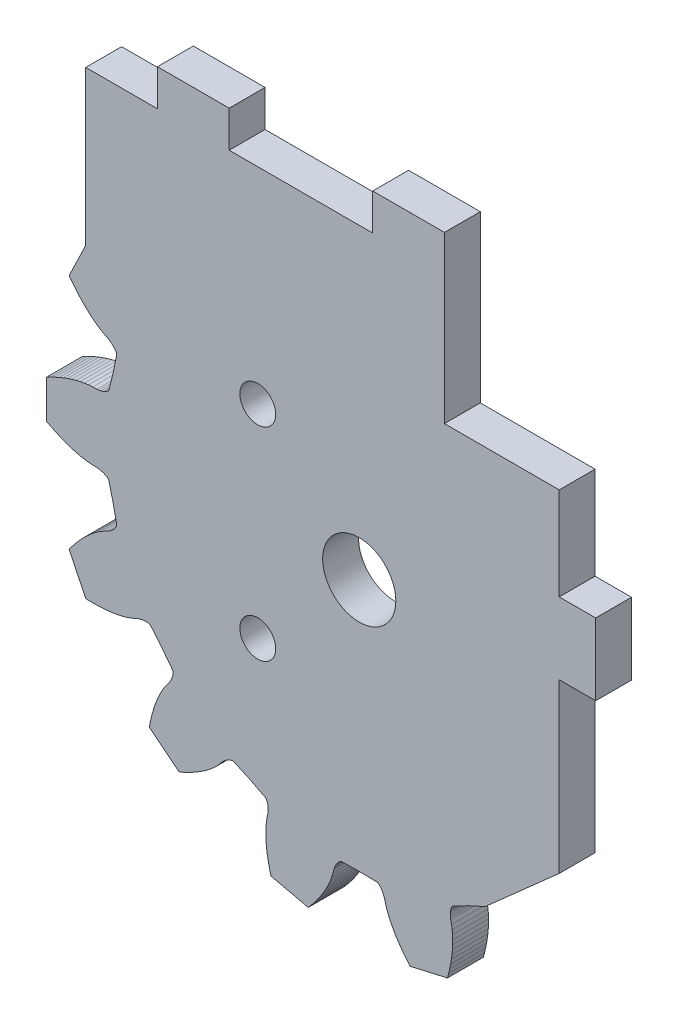
SolidWorks part; units mm, degrees
ref_plane "Front Plane" through (0, 0, 0) normal (0, 0, 1) x (1, 0, 0)
ref_plane "Top Plane" through (0, 0, 0) normal (0, 1, 0) x (1, 0, 0)
ref_plane "Right Plane" through (0, 0, 0) normal (1, 0, 0) x (0, 0, -1)
sketch "Sketch1" plane through (0, 0, 0) normal (0, 0, 1) x (1, 0, 0)
  line L0 (49.5201, 32.7081) -> (49.9074, 31.1602)
  line L1 (49.9074, 31.1602) -> (50.0141, 31.0551)
  line L2 (50.0141, 31.0551) -> (50.1157, 30.9819)
  line L3 (50.1157, 30.9819) -> (50.2145, 30.9258)
  line L4 (50.2145, 30.9258) -> (50.3116, 30.8811)
  line L5 (50.3116, 30.8811) -> (50.4073, 30.845)
  line L6 (50.4073, 30.845) -> (50.596, 30.7914)
  line L7 (50.596, 30.7914) -> (50.782, 30.7566)
  line L8 (50.782, 30.7566) -> (50.9659, 30.736)
  line L9 (50.9659, 30.736) -> (51.3296, 30.7264)
  line L10 (51.3296, 30.7264) -> (51.6946, 30.7028)
  line L11 (51.6946, 30.7028) -> (52.0629, 30.6532)
  line L12 (52.0629, 30.6532) -> (52.4332, 30.5824)
  line L13 (52.4332, 30.5824) -> (52.8051, 30.4927)
  line L14 (52.8051, 30.4927) -> (53.1779, 30.3858)
  line L15 (53.1779, 30.3858) -> (53.5516, 30.2626)
  line L16 (53.5516, 30.2626) -> (53.9257, 30.1241)
  line L17 (53.9257, 30.1241) -> (54.3001, 29.9707)
  line L18 (54.3001, 29.9707) -> (54.6743, 29.8031)
  line L19 (54.6743, 29.8031) -> (55.0479, 29.6212)
  line L20 (55.0479, 29.6212) -> (55.4208, 29.4262)
  line L21 (55.4208, 29.4262) -> (55.4208, 26.0462)
  line L22 (55.4208, 26.0462) -> (55.0479, 25.8511)
  line L23 (55.0479, 25.8511) -> (54.6743, 25.6692)
  line L24 (54.6743, 25.6692) -> (54.3001, 25.5016)
  line L25 (54.3001, 25.5016) -> (53.9257, 25.3482)
  line L26 (53.9257, 25.3482) -> (53.5516, 25.2098)
  line L27 (53.5516, 25.2098) -> (53.1779, 25.0866)
  line L28 (53.1779, 25.0866) -> (52.8051, 24.9796)
  line L29 (52.8051, 24.9796) -> (52.4332, 24.89)
  line L30 (52.4332, 24.89) -> (52.0629, 24.8191)
  line L31 (52.0629, 24.8191) -> (51.6946, 24.7693)
  line L32 (51.6946, 24.7693) -> (51.3296, 24.746)
  line L33 (51.3296, 24.746) -> (50.9659, 24.7363)
  line L34 (50.9659, 24.7363) -> (50.782, 24.7157)
  line L35 (50.782, 24.7157) -> (50.596, 24.6809)
  line L36 (50.596, 24.6809) -> (50.4073, 24.6273)
  line L37 (50.4073, 24.6273) -> (50.3116, 24.5913)
  line L38 (50.3116, 24.5913) -> (50.2145, 24.5466)
  line L39 (50.2145, 24.5466) -> (50.1157, 24.4904)
  line L40 (50.1157, 24.4904) -> (50.0141, 24.4173)
  line L41 (50.0141, 24.4173) -> (49.9074, 24.3121)
  line L42 (49.9074, 24.3121) -> (49.5201, 22.7642)
  line L43 (49.5201, 22.7642) -> (49.1973, 21.2014)
  line L44 (49.1973, 21.2014) -> (49.2481, 21.0604)
  line L45 (49.2481, 21.0604) -> (49.3077, 20.9502)
  line L46 (49.3077, 20.9502) -> (49.3725, 20.857)
  line L47 (49.3725, 20.857) -> (49.4406, 20.7747)
  line L48 (49.4406, 20.7747) -> (49.511, 20.7005)
  line L49 (49.511, 20.7005) -> (49.6578, 20.5702)
  line L50 (49.6578, 20.5702) -> (49.8102, 20.4582)
  line L51 (49.8102, 20.4582) -> (49.9669, 20.3601)
  line L52 (49.9669, 20.3601) -> (50.2905, 20.1935)
  line L53 (50.2905, 20.1935) -> (50.6092, 20.0139)
  line L54 (50.6092, 20.0139) -> (50.9194, 19.8095)
  line L55 (50.9194, 19.8095) -> (51.2224, 19.5849)
  line L56 (51.2224, 19.5849) -> (51.5183, 19.3429)
  line L57 (51.5183, 19.3429) -> (51.8081, 19.0845)
  line L58 (51.8081, 19.0845) -> (52.0913, 18.8115)
  line L59 (52.0913, 18.8115) -> (52.3682, 18.5242)
  line L60 (52.3682, 18.5242) -> (52.639, 18.2237)
  line L61 (52.639, 18.2237) -> (52.9034, 17.9103)
  line L62 (52.9034, 17.9103) -> (53.1612, 17.5844)
  line L63 (53.1612, 17.5844) -> (53.4124, 17.2469)
  line L64 (53.4124, 17.2469) -> (51.946, 14.2016)
  line L65 (51.946, 14.2016) -> (51.5252, 14.1877)
  line L66 (51.5252, 14.1877) -> (51.1099, 14.1862)
  line L67 (51.1099, 14.1862) -> (50.6999, 14.1973)
  line L68 (50.6999, 14.1973) -> (50.2961, 14.2215)
  line L69 (50.2961, 14.2215) -> (49.8991, 14.2591)
  line L70 (49.8991, 14.2591) -> (49.5089, 14.3101)
  line L71 (49.5089, 14.3101) -> (49.1264, 14.3756)
  line L72 (49.1264, 14.3756) -> (48.7525, 14.4562)
  line L73 (48.7525, 14.4562) -> (48.388, 14.5529)
  line L74 (48.388, 14.5529) -> (48.035, 14.668)
  line L75 (48.035, 14.668) -> (47.6956, 14.8054)
  line L76 (47.6956, 14.8054) -> (47.3636, 14.9542)
  line L77 (47.3636, 14.9542) -> (47.1891, 15.0157)
  line L78 (47.1891, 15.0157) -> (47.0065, 15.065)
  line L79 (47.0065, 15.065) -> (46.8135, 15.0985)
  line L80 (46.8135, 15.0985) -> (46.7114, 15.1074)
  line L81 (46.7114, 15.1074) -> (46.6047, 15.1094)
  line L82 (46.6047, 15.1094) -> (46.4914, 15.1018)
  line L83 (46.4914, 15.1018) -> (46.368, 15.0797)
  line L84 (46.368, 15.0797) -> (46.226, 15.0315)
  line L85 (46.226, 15.0315) -> (45.2056, 13.8049)
  line L86 (45.2056, 13.8049) -> (44.2366, 12.5369)
  line L87 (44.2366, 12.5369) -> (44.2211, 12.3878)
  line L88 (44.2211, 12.3878) -> (44.2272, 12.2626)
  line L89 (44.2272, 12.2626) -> (44.245, 12.1506)
  line L90 (44.245, 12.1506) -> (44.2707, 12.0467)
  line L91 (44.2707, 12.0467) -> (44.3019, 11.9494)
  line L92 (44.3019, 11.9494) -> (44.3776, 11.7686)
  line L93 (44.3776, 11.7686) -> (44.4663, 11.6014)
  line L94 (44.4663, 11.6014) -> (44.5651, 11.445)
  line L95 (44.5651, 11.445) -> (44.784, 11.1544)
  line L96 (44.784, 11.1544) -> (44.9936, 10.8544)
  line L97 (44.9936, 10.8544) -> (45.1843, 10.5357)
  line L98 (45.1843, 10.5357) -> (45.3598, 10.2019)
  line L99 (45.3598, 10.2019) -> (45.5214, 9.8552)
  line L100 (45.5214, 9.8552) -> (45.6705, 9.4971)
  line L101 (45.6705, 9.4971) -> (45.8071, 9.128)
  line L102 (45.8071, 9.128) -> (45.9321, 8.749)
  line L103 (45.9321, 8.749) -> (46.0456, 8.3609)
  line L104 (46.0456, 8.3609) -> (46.1477, 7.9637)
  line L105 (46.1477, 7.9637) -> (46.2387, 7.5583)
  line L106 (46.2387, 7.5583) -> (46.3184, 7.145)
  line L107 (46.3184, 7.145) -> (43.6761, 5.0378)
  line L108 (43.6761, 5.0378) -> (43.2907, 5.2075)
  line L109 (43.2907, 5.2075) -> (42.9158, 5.3866)
  line L110 (42.9158, 5.3866) -> (42.5516, 5.5745)
  line L111 (42.5516, 5.5745) -> (42.1983, 5.7714)
  line L112 (42.1983, 5.7714) -> (41.8567, 5.9776)
  line L113 (41.8567, 5.9776) -> (41.5272, 6.193)
  line L114 (41.5272, 6.193) -> (41.2112, 6.4178)
  line L115 (41.2112, 6.4178) -> (40.9092, 6.6528)
  line L116 (40.9092, 6.6528) -> (40.623, 6.8979)
  line L117 (40.623, 6.8979) -> (40.3545, 7.1549)
  line L118 (40.3545, 7.1549) -> (40.1086, 7.4259)
  line L119 (40.1086, 7.4259) -> (39.8742, 7.7041)
  line L120 (39.8742, 7.7041) -> (39.7436, 7.8351)
  line L121 (39.7436, 7.8351) -> (39.6004, 7.9588)
  line L122 (39.6004, 7.9588) -> (39.4409, 8.0729)
  line L123 (39.4409, 8.0729) -> (39.353, 8.125)
  line L124 (39.353, 8.125) -> (39.2575, 8.1732)
  line L125 (39.2575, 8.1732) -> (39.1521, 8.2154)
  line L126 (39.1521, 8.2154) -> (39.0314, 8.2492)
  line L127 (39.0314, 8.2492) -> (38.8826, 8.2672)
  line L128 (38.8826, 8.2672) -> (37.431, 7.6048)
  line L129 (37.431, 7.6048) -> (36.0081, 6.8829)
  line L130 (36.0081, 6.8829) -> (35.9293, 6.7551)
  line L131 (35.9293, 6.7551) -> (35.8803, 6.6398)
  line L132 (35.8803, 6.6398) -> (35.8478, 6.5311)
  line L133 (35.8478, 6.5311) -> (35.8257, 6.4265)
  line L134 (35.8257, 6.4265) -> (35.8117, 6.3251)
  line L135 (35.8117, 6.3251) -> (35.8016, 6.1293)
  line L136 (35.8016, 6.1293) -> (35.8089, 5.9403)
  line L137 (35.8089, 5.9403) -> (35.83, 5.7564)
  line L138 (35.83, 5.7564) -> (35.9014, 5.3998)
  line L139 (35.9014, 5.3998) -> (35.9598, 5.0386)
  line L140 (35.9598, 5.0386) -> (35.9933, 4.6685)
  line L141 (35.9933, 4.6685) -> (36.0065, 4.2918)
  line L142 (36.0065, 4.2918) -> (36.002, 3.9093)
  line L143 (36.002, 3.9093) -> (35.9806, 3.522)
  line L144 (35.9806, 3.522) -> (35.9438, 3.13)
  line L145 (35.9438, 3.13) -> (35.892, 2.7346)
  line L146 (35.892, 2.7346) -> (35.8257, 2.3355)
  line L147 (35.8257, 2.3355) -> (35.7454, 1.9334)
  line L148 (35.7454, 1.9334) -> (35.6514, 1.5288)
  line L149 (35.6514, 1.5288) -> (35.544, 1.1217)
  line L150 (35.544, 1.1217) -> (32.2491, 0.3696)
  line L151 (32.2491, 0.3696) -> (31.9758, 0.6896)
  line L152 (31.9758, 0.6896) -> (31.7155, 1.0137)
  line L153 (31.7155, 1.0137) -> (31.4688, 1.3411)
  line L154 (31.4688, 1.3411) -> (31.2359, 1.6718)
  line L155 (31.2359, 1.6718) -> (31.0175, 2.0058)
  line L156 (31.0175, 2.0058) -> (30.8143, 2.3426)
  line L157 (30.8143, 2.3426) -> (30.6271, 2.6825)
  line L158 (30.6271, 2.6825) -> (30.4569, 3.0251)
  line L159 (30.4569, 3.0251) -> (30.3055, 3.3703)
  line L160 (30.3055, 3.3703) -> (30.1752, 3.7181)
  line L161 (30.1752, 3.7181) -> (30.0711, 4.0691)
  line L162 (30.0711, 4.0691) -> (29.9806, 4.4214)
  line L163 (29.9806, 4.4214) -> (29.9197, 4.5961)
  line L164 (29.9197, 4.5961) -> (29.8445, 4.7696)
  line L165 (29.8445, 4.7696) -> (29.7503, 4.9416)
  line L166 (29.7503, 4.9416) -> (29.6936, 5.0269)
  line L167 (29.6936, 5.0269) -> (29.6283, 5.1115)
  line L168 (29.6283, 5.1115) -> (29.5519, 5.1953)
  line L169 (29.5519, 5.1953) -> (29.4577, 5.2781)
  line L170 (29.4577, 5.2781) -> (29.3314, 5.3589)
  line L171 (29.3314, 5.3589) -> (27.736, 5.3919)
  line L172 (27.736, 5.3919) -> (26.1409, 5.3589)
  line L173 (26.1409, 5.3589) -> (26.0147, 5.2781)
  line L174 (26.0147, 5.2781) -> (25.9204, 5.1953)
  line L175 (25.9204, 5.1953) -> (25.8437, 5.1115)
  line L176 (25.8437, 5.1115) -> (25.7787, 5.0269)
  line L177 (25.7787, 5.0269) -> (25.7221, 4.9416)
  line L178 (25.7221, 4.9416) -> (25.6278, 4.7696)
  line L179 (25.6278, 4.7696) -> (25.5527, 4.5961)
  line L180 (25.5527, 4.5961) -> (25.4917, 4.4214)
  line L181 (25.4917, 4.4214) -> (25.4013, 4.0691)
  line L182 (25.4013, 4.0691) -> (25.2971, 3.7181)
  line L183 (25.2971, 3.7181) -> (25.1668, 3.3703)
  line L184 (25.1668, 3.3703) -> (25.0154, 3.0251)
  line L185 (25.0154, 3.0251) -> (24.8453, 2.6825)
  line L186 (24.8453, 2.6825) -> (24.6581, 2.3426)
  line L187 (24.6581, 2.3426) -> (24.4549, 2.0058)
  line L188 (24.4549, 2.0058) -> (24.2364, 1.6718)
  line L189 (24.2364, 1.6718) -> (24.0035, 1.3411)
  line L190 (24.0035, 1.3411) -> (23.7569, 1.0137)
  line L191 (23.7569, 1.0137) -> (23.4965, 0.6896)
  line L192 (23.4965, 0.6896) -> (23.2232, 0.3696)
  line L193 (23.2232, 0.3696) -> (19.9283, 1.1217)
  line L194 (19.9283, 1.1217) -> (19.8209, 1.5288)
  line L195 (19.8209, 1.5288) -> (19.7269, 1.9334)
  line L196 (19.7269, 1.9334) -> (19.6466, 2.3355)
  line L197 (19.6466, 2.3355) -> (19.5804, 2.7346)
  line L198 (19.5804, 2.7346) -> (19.5285, 3.13)
  line L199 (19.5285, 3.13) -> (19.4917, 3.522)
  line L200 (19.4917, 3.522) -> (19.4704, 3.9093)
  line L201 (19.4704, 3.9093) -> (19.4658, 4.2918)
  line L202 (19.4658, 4.2918) -> (19.479, 4.6685)
  line L203 (19.479, 4.6685) -> (19.5125, 5.0386)
  line L204 (19.5125, 5.0386) -> (19.571, 5.3998)
  line L205 (19.571, 5.3998) -> (19.6423, 5.7564)
  line L206 (19.6423, 5.7564) -> (19.6634, 5.9403)
  line L207 (19.6634, 5.9403) -> (19.6708, 6.1293)
  line L208 (19.6708, 6.1293) -> (19.6606, 6.3251)
  line L209 (19.6606, 6.3251) -> (19.6466, 6.4265)
  line L210 (19.6466, 6.4265) -> (19.6245, 6.5311)
  line L211 (19.6245, 6.5311) -> (19.592, 6.6398)
  line L212 (19.592, 6.6398) -> (19.543, 6.7551)
  line L213 (19.543, 6.7551) -> (19.4643, 6.8829)
  line L214 (19.4643, 6.8829) -> (18.0414, 7.6048)
  line L215 (18.0414, 7.6048) -> (16.5898, 8.2672)
  line L216 (16.5898, 8.2672) -> (16.4409, 8.2492)
  line L217 (16.4409, 8.2492) -> (16.3203, 8.2154)
  line L218 (16.3203, 8.2154) -> (16.2149, 8.1732)
  line L219 (16.2149, 8.1732) -> (16.1193, 8.125)
  line L220 (16.1193, 8.125) -> (16.0315, 8.0729)
  line L221 (16.0315, 8.0729) -> (15.872, 7.9588)
  line L222 (15.872, 7.9588) -> (15.7287, 7.8351)
  line L223 (15.7287, 7.8351) -> (15.5981, 7.7041)
  line L224 (15.5981, 7.7041) -> (15.3637, 7.4259)
  line L225 (15.3637, 7.4259) -> (15.1178, 7.1549)
  line L226 (15.1178, 7.1549) -> (14.8493, 6.8979)
  line L227 (14.8493, 6.8979) -> (14.5631, 6.6528)
  line L228 (14.5631, 6.6528) -> (14.2611, 6.4178)
  line L229 (14.2611, 6.4178) -> (13.9451, 6.193)
  line L230 (13.9451, 6.193) -> (13.6157, 5.9776)
  line L231 (13.6157, 5.9776) -> (13.274, 5.7714)
  line L232 (13.274, 5.7714) -> (12.9207, 5.5745)
  line L233 (12.9207, 5.5745) -> (12.5565, 5.3866)
  line L234 (12.5565, 5.3866) -> (12.1816, 5.2075)
  line L235 (12.1816, 5.2075) -> (11.7963, 5.0378)
  line L236 (11.7963, 5.0378) -> (9.1539, 7.145)
  line L237 (9.1539, 7.145) -> (9.2337, 7.5583)
  line L238 (9.2337, 7.5583) -> (9.3246, 7.9637)
  line L239 (9.3246, 7.9637) -> (9.4267, 8.3609)
  line L240 (9.4267, 8.3609) -> (9.5402, 8.749)
  line L241 (9.5402, 8.749) -> (9.6652, 9.128)
  line L242 (9.6652, 9.128) -> (9.8019, 9.4971)
  line L243 (9.8019, 9.4971) -> (9.951, 9.8552)
  line L244 (9.951, 9.8552) -> (10.1125, 10.2019)
  line L245 (10.1125, 10.2019) -> (10.288, 10.5357)
  line L246 (10.288, 10.5357) -> (10.4788, 10.8544)
  line L247 (10.4788, 10.8544) -> (10.6883, 11.1544)
  line L248 (10.6883, 11.1544) -> (10.9073, 11.445)
  line L249 (10.9073, 11.445) -> (11.0058, 11.6014)
  line L250 (11.0058, 11.6014) -> (11.0947, 11.7686)
  line L251 (11.0947, 11.7686) -> (11.1704, 11.9494)
  line L252 (11.1704, 11.9494) -> (11.2017, 12.0467)
  line L253 (11.2017, 12.0467) -> (11.2273, 12.1506)
  line L254 (11.2273, 12.1506) -> (11.2451, 12.2626)
  line L255 (11.2451, 12.2626) -> (11.2512, 12.3878)
  line L256 (11.2512, 12.3878) -> (11.2354, 12.5369)
  line L257 (11.2354, 12.5369) -> (10.2667, 13.8049)
  line L258 (10.2667, 13.8049) -> (9.2464, 15.0315)
  line L259 (9.2464, 15.0315) -> (9.1044, 15.0797)
  line L260 (9.1044, 15.0797) -> (8.9809, 15.1018)
  line L261 (8.9809, 15.1018) -> (8.8676, 15.1094)
  line L262 (8.8676, 15.1094) -> (8.761, 15.1074)
  line L263 (8.761, 15.1074) -> (8.6589, 15.0985)
  line L264 (8.6589, 15.0985) -> (8.4658, 15.065)
  line L265 (8.4658, 15.065) -> (8.2832, 15.0157)
  line L266 (8.2832, 15.0157) -> (8.1087, 14.9542)
  line L267 (8.1087, 14.9542) -> (7.7767, 14.8054)
  line L268 (7.7767, 14.8054) -> (7.4374, 14.668)
  line L269 (7.4374, 14.668) -> (7.0843, 14.5529)
  line L270 (7.0843, 14.5529) -> (6.7198, 14.4562)
  line L271 (6.7198, 14.4562) -> (6.3459, 14.3756)
  line L272 (6.3459, 14.3756) -> (5.9634, 14.3101)
  line L273 (5.9634, 14.3101) -> (5.5733, 14.2591)
  line L274 (5.5733, 14.2591) -> (5.1763, 14.2215)
  line L275 (5.1763, 14.2215) -> (4.7724, 14.1973)
  line L276 (4.7724, 14.1973) -> (4.3624, 14.1862)
  line L277 (4.3624, 14.1862) -> (3.9472, 14.1877)
  line L278 (3.9472, 14.1877) -> (3.5263, 14.2016)
  line L279 (3.5263, 14.2016) -> (2.0599, 17.2469)
  line L280 (2.0599, 17.2469) -> (2.3111, 17.5844)
  line L281 (2.3111, 17.5844) -> (2.569, 17.9103)
  line L282 (2.569, 17.9103) -> (2.8334, 18.2237)
  line L283 (2.8334, 18.2237) -> (3.1041, 18.5242)
  line L284 (3.1041, 18.5242) -> (3.381, 18.8115)
  line L285 (3.381, 18.8115) -> (3.6642, 19.0845)
  line L286 (3.6642, 19.0845) -> (3.954, 19.3429)
  line L287 (3.954, 19.3429) -> (4.2499, 19.5849)
  line L288 (4.2499, 19.5849) -> (4.553, 19.8095)
  line L289 (4.553, 19.8095) -> (4.8631, 20.0139)
  line L290 (4.8631, 20.0139) -> (5.1819, 20.1935)
  line L291 (5.1819, 20.1935) -> (5.5054, 20.3601)
  line L292 (5.5054, 20.3601) -> (5.6622, 20.4582)
  line L293 (5.6622, 20.4582) -> (5.8146, 20.5702)
  line L294 (5.8146, 20.5702) -> (5.9614, 20.7005)
  line L295 (5.9614, 20.7005) -> (6.0317, 20.7747)
  line L296 (6.0317, 20.7747) -> (6.0998, 20.857)
  line L297 (6.0998, 20.857) -> (6.1646, 20.9502)
  line L298 (6.1646, 20.9502) -> (6.2243, 21.0604)
  line L299 (6.2243, 21.0604) -> (6.2748, 21.2014)
  line L300 (6.2748, 21.2014) -> (5.9522, 22.7642)
  line L301 (5.9522, 22.7642) -> (5.5649, 24.3121)
  line L302 (5.5649, 24.3121) -> (5.4582, 24.4173)
  line L303 (5.4582, 24.4173) -> (5.3566, 24.4904)
  line L304 (5.3566, 24.4904) -> (5.2578, 24.5466)
  line L305 (5.2578, 24.5466) -> (5.1608, 24.5913)
  line L306 (5.1608, 24.5913) -> (5.065, 24.6273)
  line L307 (5.065, 24.6273) -> (4.8763, 24.6809)
  line L308 (4.8763, 24.6809) -> (4.6904, 24.7157)
  line L309 (4.6904, 24.7157) -> (4.5065, 24.7363)
  line L310 (4.5065, 24.7363) -> (4.1427, 24.746)
  line L311 (4.1427, 24.746) -> (3.7777, 24.7693)
  line L312 (3.7777, 24.7693) -> (3.4094, 24.8191)
  line L313 (3.4094, 24.8191) -> (3.0391, 24.89)
  line L314 (3.0391, 24.89) -> (2.6673, 24.9796)
  line L315 (2.6673, 24.9796) -> (2.2944, 25.0866)
  line L316 (2.2944, 25.0866) -> (1.9207, 25.2098)
  line L317 (1.9207, 25.2098) -> (1.5466, 25.3482)
  line L318 (1.5466, 25.3482) -> (1.1722, 25.5016)
  line L319 (1.1722, 25.5016) -> (0.7981, 25.6692)
  line L320 (0.7981, 25.6692) -> (0.4244, 25.8511)
  line L321 (0.4244, 25.8511) -> (0.0516, 26.0462)
  line L322 (0.0516, 26.0462) -> (0.0516, 29.4262)
  line L323 (0.0516, 29.4262) -> (0.4244, 29.6212)
  line L324 (0.4244, 29.6212) -> (0.7981, 29.8031)
  line L325 (0.7981, 29.8031) -> (1.1722, 29.9707)
  line L326 (1.1722, 29.9707) -> (1.5466, 30.1241)
  line L327 (1.5466, 30.1241) -> (1.9207, 30.2626)
  line L328 (1.9207, 30.2626) -> (2.2944, 30.3858)
  line L329 (2.2944, 30.3858) -> (2.6673, 30.4927)
  line L330 (2.6673, 30.4927) -> (3.0391, 30.5824)
  line L331 (3.0391, 30.5824) -> (3.4094, 30.6532)
  line L332 (3.4094, 30.6532) -> (3.7777, 30.7028)
  line L333 (3.7777, 30.7028) -> (4.1427, 30.7264)
  line L334 (4.1427, 30.7264) -> (4.5065, 30.736)
  line L335 (4.5065, 30.736) -> (4.6904, 30.7566)
  line L336 (4.6904, 30.7566) -> (4.8763, 30.7914)
  line L337 (4.8763, 30.7914) -> (5.065, 30.845)
  line L338 (5.065, 30.845) -> (5.1608, 30.8811)
  line L339 (5.1608, 30.8811) -> (5.2578, 30.9258)
  line L340 (5.2578, 30.9258) -> (5.3566, 30.9819)
  line L341 (5.3566, 30.9819) -> (5.4582, 31.0551)
  line L342 (5.4582, 31.0551) -> (5.5649, 31.1602)
  line L343 (5.5649, 31.1602) -> (5.9522, 32.7081)
  line L344 (5.9522, 32.7081) -> (6.2748, 34.2709)
  line L345 (6.2748, 34.2709) -> (6.2243, 34.4119)
  line L346 (6.2243, 34.4119) -> (6.1646, 34.5222)
  line L347 (6.1646, 34.5222) -> (6.0998, 34.6154)
  line L348 (6.0998, 34.6154) -> (6.0317, 34.6977)
  line L349 (6.0317, 34.6977) -> (5.9614, 34.7718)
  line L350 (5.9614, 34.7718) -> (5.8146, 34.9021)
  line L351 (5.8146, 34.9021) -> (5.6622, 35.0142)
  line L352 (5.6622, 35.0142) -> (5.5054, 35.1122)
  line L353 (5.5054, 35.1122) -> (5.1819, 35.2788)
  line L354 (5.1819, 35.2788) -> (4.8631, 35.4584)
  line L355 (4.8631, 35.4584) -> (4.553, 35.6629)
  line L356 (4.553, 35.6629) -> (4.2499, 35.8874)
  line L357 (4.2499, 35.8874) -> (3.954, 36.1295)
  line L358 (3.954, 36.1295) -> (3.6642, 36.3878)
  line L359 (3.6642, 36.3878) -> (3.381, 36.6608)
  line L360 (3.381, 36.6608) -> (3.1041, 36.9481)
  line L361 (3.1041, 36.9481) -> (2.8334, 37.2486)
  line L362 (2.8334, 37.2486) -> (2.569, 37.562)
  line L363 (2.569, 37.562) -> (2.3111, 37.8879)
  line L364 (2.3111, 37.8879) -> (2.0599, 38.2255)
  line L365 (2.0599, 38.2255) -> (3.5263, 41.2707)
  line L366 (3.5263, 41.2707) -> (3.9472, 41.2847)
  line L367 (3.9472, 41.2847) -> (4.3624, 41.2862)
  line L368 (4.3624, 41.2862) -> (4.7724, 41.275)
  line L369 (4.7724, 41.275) -> (5.1763, 41.2509)
  line L370 (5.1763, 41.2509) -> (5.5733, 41.2133)
  line L371 (5.5733, 41.2133) -> (5.9634, 41.1622)
  line L372 (5.9634, 41.1622) -> (6.3459, 41.0967)
  line L373 (6.3459, 41.0967) -> (6.7198, 41.0162)
  line L374 (6.7198, 41.0162) -> (7.0843, 40.9194)
  line L375 (7.0843, 40.9194) -> (7.4374, 40.8043)
  line L376 (7.4374, 40.8043) -> (7.7767, 40.6669)
  line L377 (7.7767, 40.6669) -> (8.1087, 40.5181)
  line L378 (8.1087, 40.5181) -> (8.2832, 40.4566)
  line L379 (8.2832, 40.4566) -> (8.4658, 40.4073)
  line L380 (8.4658, 40.4073) -> (8.6589, 40.3738)
  line L381 (8.6589, 40.3738) -> (8.761, 40.3649)
  line L382 (8.761, 40.3649) -> (8.8676, 40.3629)
  line L383 (8.8676, 40.3629) -> (8.9809, 40.3705)
  line L384 (8.9809, 40.3705) -> (9.1044, 40.3926)
  line L385 (9.1044, 40.3926) -> (9.2464, 40.4409)
  line L386 (9.2464, 40.4409) -> (10.2667, 41.6674)
  line L387 (10.2667, 41.6674) -> (11.2354, 42.9354)
  line L388 (11.2354, 42.9354) -> (11.2512, 43.0845)
  line L389 (11.2512, 43.0845) -> (11.2451, 43.2097)
  line L390 (11.2451, 43.2097) -> (11.2273, 43.3217)
  line L391 (11.2273, 43.3217) -> (11.2017, 43.4256)
  line L392 (11.2017, 43.4256) -> (11.1704, 43.5229)
  line L393 (11.1704, 43.5229) -> (11.0947, 43.7037)
  line L394 (11.0947, 43.7037) -> (11.0058, 43.8709)
  line L395 (11.0058, 43.8709) -> (10.9073, 44.0273)
  line L396 (10.9073, 44.0273) -> (10.6883, 44.3179)
  line L397 (10.6883, 44.3179) -> (10.4788, 44.6179)
  line L398 (10.4788, 44.6179) -> (10.288, 44.9367)
  line L399 (10.288, 44.9367) -> (10.1125, 45.2704)
  line L400 (10.1125, 45.2704) -> (9.951, 45.6171)
  line L401 (9.951, 45.6171) -> (9.8019, 45.9753)
  line L402 (9.8019, 45.9753) -> (9.6652, 46.3443)
  line L403 (9.6652, 46.3443) -> (9.5402, 46.7233)
  line L404 (9.5402, 46.7233) -> (9.4267, 47.1114)
  line L405 (9.4267, 47.1114) -> (9.3246, 47.5087)
  line L406 (9.3246, 47.5087) -> (9.2337, 47.9141)
  line L407 (9.2337, 47.9141) -> (9.1539, 48.3273)
  line L408 (9.1539, 48.3273) -> (11.7963, 50.4345)
  line L409 (11.7963, 50.4345) -> (12.1816, 50.2648)
  line L410 (12.1816, 50.2648) -> (12.5565, 50.0858)
  line L411 (12.5565, 50.0858) -> (12.9207, 49.8978)
  line L412 (12.9207, 49.8978) -> (13.274, 49.7009)
  line L413 (13.274, 49.7009) -> (13.6157, 49.4947)
  line L414 (13.6157, 49.4947) -> (13.9451, 49.2793)
  line L415 (13.9451, 49.2793) -> (14.2611, 49.0545)
  line L416 (14.2611, 49.0545) -> (14.5631, 48.8196)
  line L417 (14.5631, 48.8196) -> (14.8493, 48.5745)
  line L418 (14.8493, 48.5745) -> (15.1178, 48.3174)
  line L419 (15.1178, 48.3174) -> (15.3637, 48.0464)
  line L420 (15.3637, 48.0464) -> (15.5981, 47.7683)
  line L421 (15.5981, 47.7683) -> (15.7287, 47.6372)
  line L422 (15.7287, 47.6372) -> (15.872, 47.5135)
  line L423 (15.872, 47.5135) -> (16.0315, 47.3994)
  line L424 (16.0315, 47.3994) -> (16.1193, 47.3471)
  line L425 (16.1193, 47.3471) -> (16.2149, 47.2991)
  line L426 (16.2149, 47.2991) -> (16.3203, 47.257)
  line L427 (16.3203, 47.257) -> (16.4409, 47.2232)
  line L428 (16.4409, 47.2232) -> (16.5898, 47.2051)
  line L429 (16.5898, 47.2051) -> (18.0414, 47.8676)
  line L430 (18.0414, 47.8676) -> (19.4643, 48.5894)
  line L431 (19.4643, 48.5894) -> (19.543, 48.7172)
  line L432 (19.543, 48.7172) -> (19.592, 48.8325)
  line L433 (19.592, 48.8325) -> (19.6245, 48.9412)
  line L434 (19.6245, 48.9412) -> (19.6466, 49.0459)
  line L435 (19.6466, 49.0459) -> (19.6606, 49.1472)
  line L436 (19.6606, 49.1472) -> (19.6708, 49.3431)
  line L437 (19.6708, 49.3431) -> (19.6634, 49.532)
  line L438 (19.6634, 49.532) -> (19.6423, 49.7159)
  line L439 (19.6423, 49.7159) -> (19.571, 50.0725)
  line L440 (19.571, 50.0725) -> (19.5125, 50.4337)
  line L441 (19.5125, 50.4337) -> (19.479, 50.8038)
  line L442 (19.479, 50.8038) -> (19.4658, 51.1805)
  line L443 (19.4658, 51.1805) -> (19.4704, 51.563)
  line L444 (19.4704, 51.563) -> (19.4917, 51.9504)
  line L445 (19.4917, 51.9504) -> (19.5285, 52.3423)
  line L446 (19.5285, 52.3423) -> (19.5804, 52.7378)
  line L447 (19.5804, 52.7378) -> (19.8209, 52.7378)
  line L448 (19.8209, 52.7378) -> (20.3725, 53.1297)
  line L449 (20.3725, 53.1297) -> (21.0344, 53.4665)
  line L450 (21.0344, 53.4665) -> (21.4927, 53.8005)
  line L451 (21.4927, 53.8005) -> (22.3582, 54.1312)
  line L452 (22.3582, 54.1312) -> (23.2232, 54.1312)
  line L453 (23.2232, 54.1312) -> (23.7569, 54.1312)
  line L454 (23.7569, 54.1312) -> (24.0035, 54.1312)
  line L455 (24.0035, 54.1312) -> (24.2364, 53.8005)
  line L456 (24.2364, 53.8005) -> (24.4549, 53.4665)
  line L457 (24.4549, 53.4665) -> (24.6581, 53.1297)
  line L458 (24.6581, 53.1297) -> (24.8453, 52.7898)
  line L459 (24.8453, 52.7898) -> (25.0154, 52.4472)
  line L460 (25.0154, 52.4472) -> (25.1668, 52.102)
  line L461 (25.1668, 52.102) -> (25.2971, 51.754)
  line L462 (25.2971, 51.754) -> (25.4013, 51.4033)
  line L463 (25.4013, 51.4033) -> (25.4917, 51.051)
  line L464 (25.4917, 51.051) -> (25.5527, 50.8762)
  line L465 (25.5527, 50.8762) -> (25.6278, 50.7027)
  line L466 (25.6278, 50.7027) -> (25.7221, 50.5308)
  line L467 (25.7221, 50.5308) -> (25.7787, 50.4454)
  line L468 (25.7787, 50.4454) -> (25.8437, 50.3608)
  line L469 (25.8437, 50.3608) -> (25.9204, 50.277)
  line L470 (25.9204, 50.277) -> (26.0147, 50.1942)
  line L471 (26.0147, 50.1942) -> (26.1409, 50.1134)
  line L472 (26.1409, 50.1134) -> (27.736, 50.0804)
  line L473 (27.736, 50.0804) -> (29.3314, 50.1134)
  line L474 (29.3314, 50.1134) -> (29.4577, 50.1942)
  line L475 (29.4577, 50.1942) -> (29.5519, 50.277)
  line L476 (29.5519, 50.277) -> (29.6283, 50.3608)
  line L477 (29.6283, 50.3608) -> (29.6936, 50.4454)
  line L478 (29.6936, 50.4454) -> (29.7503, 50.5308)
  line L479 (29.7503, 50.5308) -> (29.8445, 50.7027)
  line L480 (29.8445, 50.7027) -> (29.9197, 50.8762)
  line L481 (29.9197, 50.8762) -> (29.9806, 51.051)
  line L482 (29.9806, 51.051) -> (30.0711, 51.4033)
  line L483 (30.0711, 51.4033) -> (30.1752, 51.754)
  line L484 (30.1752, 51.754) -> (30.3055, 52.102)
  line L485 (30.3055, 52.102) -> (30.4569, 52.4472)
  line L486 (30.4569, 52.4472) -> (30.6271, 52.7898)
  line L487 (30.6271, 52.7898) -> (30.8143, 53.1297)
  line L488 (30.8143, 53.1297) -> (31.0175, 53.4665)
  line L489 (31.0175, 53.4665) -> (31.2359, 53.8005)
  line L490 (31.2359, 53.8005) -> (31.4688, 54.1312)
  line L491 (31.4688, 54.1312) -> (31.9758, 53.8005)
  line L492 (31.9758, 53.8005) -> (32.7958, 53.8005)
  line L493 (32.7958, 53.8005) -> (33.7632, 53.8005)
  line L494 (33.7632, 53.8005) -> (34.6287, 53.8005)
  line L495 (34.6287, 53.8005) -> (35.4434, 53.6108)
  line L496 (35.4434, 53.6108) -> (35.7454, 53.5389)
  line L497 (35.7454, 53.5389) -> (35.8257, 53.1368)
  line L498 (35.8257, 53.1368) -> (35.892, 52.7378)
  line L499 (35.892, 52.7378) -> (35.9438, 52.3423)
  line L500 (35.9438, 52.3423) -> (35.9806, 51.9504)
  line L501 (35.9806, 51.9504) -> (36.002, 51.563)
  line L502 (36.002, 51.563) -> (36.0065, 51.1805)
  line L503 (36.0065, 51.1805) -> (35.9933, 50.8038)
  line L504 (35.9933, 50.8038) -> (35.9598, 50.4337)
  line L505 (35.9598, 50.4337) -> (35.9014, 50.0725)
  line L506 (35.9014, 50.0725) -> (35.83, 49.7159)
  line L507 (35.83, 49.7159) -> (35.8089, 49.532)
  line L508 (35.8089, 49.532) -> (35.8016, 49.3431)
  line L509 (35.8016, 49.3431) -> (35.8117, 49.1472)
  line L510 (35.8117, 49.1472) -> (35.8257, 49.0459)
  line L511 (35.8257, 49.0459) -> (35.8478, 48.9412)
  line L512 (35.8478, 48.9412) -> (35.8803, 48.8325)
  line L513 (35.8803, 48.8325) -> (35.9293, 48.7172)
  line L514 (35.9293, 48.7172) -> (36.0081, 48.5894)
  line L515 (36.0081, 48.5894) -> (37.431, 47.8676)
  line L516 (37.431, 47.8676) -> (38.8826, 47.2051)
  line L517 (38.8826, 47.2051) -> (39.0314, 47.2232)
  line L518 (39.0314, 47.2232) -> (39.1521, 47.257)
  line L519 (39.1521, 47.257) -> (39.2575, 47.2991)
  line L520 (39.2575, 47.2991) -> (39.353, 47.3471)
  line L521 (39.353, 47.3471) -> (39.4409, 47.3994)
  line L522 (39.4409, 47.3994) -> (39.6004, 47.5135)
  line L523 (39.6004, 47.5135) -> (39.7436, 47.6372)
  line L524 (39.7436, 47.6372) -> (39.8742, 47.7683)
  line L525 (39.8742, 47.7683) -> (40.1086, 48.0464)
  line L526 (40.1086, 48.0464) -> (40.3545, 48.3174)
  line L527 (40.3545, 48.3174) -> (40.623, 48.5745)
  line L528 (40.623, 48.5745) -> (40.9092, 48.8196)
  line L529 (40.9092, 48.8196) -> (41.2112, 49.0545)
  line L530 (41.2112, 49.0545) -> (41.5272, 49.2793)
  line L531 (41.5272, 49.2793) -> (41.8567, 49.4947)
  line L532 (41.8567, 49.4947) -> (42.1983, 49.7009)
  line L533 (42.1983, 49.7009) -> (42.5516, 49.8978)
  line L534 (42.5516, 49.8978) -> (42.9158, 50.0858)
  line L535 (42.9158, 50.0858) -> (43.2907, 50.2648)
  line L536 (43.2907, 50.2648) -> (43.6761, 50.4345)
  line L537 (43.6761, 50.4345) -> (46.3184, 48.3273)
  line L538 (46.3184, 48.3273) -> (46.2387, 47.9141)
  line L539 (46.2387, 47.9141) -> (46.1477, 47.5087)
  line L540 (46.1477, 47.5087) -> (46.0456, 47.1114)
  line L541 (46.0456, 47.1114) -> (45.9321, 46.7233)
  line L542 (45.9321, 46.7233) -> (45.8071, 46.3443)
  line L543 (45.8071, 46.3443) -> (45.6705, 45.9753)
  line L544 (45.6705, 45.9753) -> (45.5214, 45.6171)
  line L545 (45.5214, 45.6171) -> (45.3598, 45.2704)
  line L546 (45.3598, 45.2704) -> (45.1843, 44.9367)
  line L547 (45.1843, 44.9367) -> (44.9936, 44.6179)
  line L548 (44.9936, 44.6179) -> (44.784, 44.3179)
  line L549 (44.784, 44.3179) -> (44.5651, 44.0273)
  line L550 (44.5651, 44.0273) -> (44.4663, 43.8709)
  line L551 (44.4663, 43.8709) -> (44.3776, 43.7037)
  line L552 (44.3776, 43.7037) -> (44.3019, 43.5229)
  line L553 (44.3019, 43.5229) -> (44.2707, 43.4256)
  line L554 (44.2707, 43.4256) -> (44.245, 43.3217)
  line L555 (44.245, 43.3217) -> (44.2272, 43.2097)
  line L556 (44.2272, 43.2097) -> (44.2211, 43.0845)
  line L557 (44.2211, 43.0845) -> (44.2366, 42.9354)
  line L558 (44.2366, 42.9354) -> (45.2056, 41.6674)
  line L559 (45.2056, 41.6674) -> (46.226, 40.4409)
  line L560 (46.226, 40.4409) -> (46.368, 40.3926)
  line L561 (46.368, 40.3926) -> (46.4914, 40.3705)
  line L562 (46.4914, 40.3705) -> (46.6047, 40.3629)
  line L563 (46.6047, 40.3629) -> (46.7114, 40.3649)
  line L564 (46.7114, 40.3649) -> (46.8135, 40.3738)
  line L565 (46.8135, 40.3738) -> (47.0065, 40.4073)
  line L566 (47.0065, 40.4073) -> (47.1891, 40.4566)
  line L567 (47.1891, 40.4566) -> (47.3636, 40.5181)
  line L568 (47.3636, 40.5181) -> (47.6956, 40.6669)
  line L569 (47.6956, 40.6669) -> (48.035, 40.8043)
  line L570 (48.035, 40.8043) -> (48.388, 40.9194)
  line L571 (48.388, 40.9194) -> (48.7525, 41.0162)
  line L572 (48.7525, 41.0162) -> (49.1264, 41.0967)
  line L573 (49.1264, 41.0967) -> (49.5089, 41.1622)
  line L574 (49.5089, 41.1622) -> (49.8991, 41.2133)
  line L575 (49.8991, 41.2133) -> (50.2961, 41.2509)
  line L576 (50.2961, 41.2509) -> (50.6999, 41.275)
  line L577 (50.6999, 41.275) -> (51.1099, 41.2862)
  line L578 (51.1099, 41.2862) -> (51.5252, 41.2847)
  line L579 (51.5252, 41.2847) -> (51.946, 41.2707)
  line L580 (51.946, 41.2707) -> (53.4124, 38.2255)
  line L581 (53.4124, 38.2255) -> (53.1612, 37.8879)
  line L582 (53.1612, 37.8879) -> (52.9034, 37.562)
  line L583 (52.9034, 37.562) -> (52.639, 37.2486)
  line L584 (52.639, 37.2486) -> (52.3682, 36.9481)
  line L585 (52.3682, 36.9481) -> (52.0913, 36.6608)
  line L586 (52.0913, 36.6608) -> (51.8081, 36.3878)
  line L587 (51.8081, 36.3878) -> (51.5183, 36.1295)
  line L588 (51.5183, 36.1295) -> (51.2224, 35.8874)
  line L589 (51.2224, 35.8874) -> (50.9194, 35.6629)
  line L590 (50.9194, 35.6629) -> (50.6092, 35.4584)
  line L591 (50.6092, 35.4584) -> (50.2905, 35.2788)
  line L592 (50.2905, 35.2788) -> (49.9669, 35.1122)
  line L593 (49.9669, 35.1122) -> (49.8102, 35.0142)
  line L594 (49.8102, 35.0142) -> (49.6578, 34.9021)
  line L595 (49.6578, 34.9021) -> (49.511, 34.7718)
  line L596 (49.511, 34.7718) -> (49.4406, 34.6977)
  line L597 (49.4406, 34.6977) -> (49.3725, 34.6154)
  line L598 (49.3725, 34.6154) -> (49.3077, 34.5222)
  line L599 (49.3077, 34.5222) -> (49.2481, 34.4119)
  line L600 (49.2481, 34.4119) -> (49.1973, 34.2709)
  line L601 (49.1973, 34.2709) -> (49.5201, 32.7081)
  circle A0 centre (27.736, 27.736) radius 3.2385
  dimension "D1" = 6.477
extrude "Boss-Extrude1" add sketch "Sketch1" along normal blind 3.175
sketch "Sketch2" plane through (0, 0, 3.175) normal (0, 0, 1) x (1, 0, 0)
  line L0 (3.5263, 41.2707) -> (3.5263, 54.914)
  line L1 (46.226, 15.0315) -> (46.226, 54.914)
  line L2 (46.226, 54.914) -> (3.5263, 54.914)
  line L3 (3.5263, 41.2707) -> (21.5802, 32.844)
  line L4 (21.5802, 32.844) -> (34.6099, 32.844)
  line L5 (34.6099, 32.844) -> (46.226, 15.0315)
  circle A0 centre (27.736, 27.736) radius 3.2385 construction
  dimension "D1" = 27.178
  dimension "D2" = 42.6997
extrude "Boss-Extrude2" add sketch "Sketch2" against normal blind 3.175
sketch "Sketch3" plane through (0, 0, 3.175) normal (0, 0, 1) x (1, 0, 0)
  line L0 (45.4363, 54.914) -> (45.4363, -3.0965)
  line L1 (46.226, 54.914) -> (3.5263, 54.914) construction
  line L2 (45.4363, -3.0965) -> (75.4048, -3.0965)
  line L3 (45.4363, 54.914) -> (75.4048, 54.914)
  line L4 (75.4048, 54.914) -> (75.4048, -3.0965)
  line L5 (3.5263, 54.914) -> (3.5263, 41.2707) construction
  dimension "D1" = 41.91
extrude "Cut-Extrude1" cut sketch "Sketch3" against normal through all
sketch "Sketch4" plane through (0, 0, 3.175) normal (0, 0, 1) x (1, 0, 0)
  line L1 (45.4363, 54.914) -> (45.4363, 14.0822) construction
  line L6 (35.2763, 54.914) -> (35.2763, 43.484)
  line L7 (45.4363, 54.914) -> (3.5263, 54.914) construction
  line L8 (35.2763, 43.484) -> (45.4363, 43.484)
  line L9 (45.4363, 43.484) -> (45.4363, 54.914)
  line L10 (45.4363, 54.914) -> (35.2763, 54.914)
  dimension "D4" = 11.43
  dimension "D5" = 10.16
extrude "Cut-Extrude2" cut sketch "Sketch4" against normal through all
sketch "Sketch5" plane through (0, 0, 3.175) normal (0, 0, 1) x (1, 0, 0)
  line L0 (9.8763, 54.914) -> (9.8763, 58.1398)
  line L1 (35.2763, 54.914) -> (3.5263, 54.914) construction
  line L2 (9.8763, 58.1398) -> (16.2263, 58.1398)
  line L3 (16.2263, 58.1398) -> (16.2263, 54.914)
  line L4 (16.2263, 54.914) -> (9.8763, 54.914)
  line L5 (28.9263, 54.914) -> (28.9263, 58.1398)
  line L6 (28.9263, 58.1398) -> (35.2763, 58.1398)
  line L7 (35.2763, 58.1398) -> (35.2763, 54.914)
  line L8 (35.2763, 54.914) -> (28.9263, 54.914)
  line L9 (3.5263, 54.914) -> (3.5263, 41.2707) construction
  line L10 (45.4363, 35.2789) -> (48.6621, 35.2789)
  line L11 (45.4363, 43.484) -> (45.4363, 14.0822) construction
  line L12 (48.6621, 35.2789) -> (48.6621, 28.9289)
  line L13 (48.6621, 28.9289) -> (45.4363, 28.9289)
  line L14 (45.4363, 28.9289) -> (45.4363, 35.2789)
  line L15 (48.6621, 32.1039) -> (46.5949, 32.1039) construction
  line L16 (45.4363, 32.1039) -> (46.5949, 32.1039) construction
  dimension "D1" = 3.2258
  dimension "D2" = 6.35
  dimension "D3" = 6.35
  dimension "D4" = 3.2258
  dimension "D5" = 12.7
  dimension "D6" = 6.35
  dimension "D7" = 6.35
  dimension "D8" = 3.2258
extrude "tabs" add sketch "Sketch5" against normal blind 3.175
sketch "Sketch6" plane through (0, 0, 3.175) normal (0, 0, 1) x (1, 0, 0)
  line L0 (27.736, 27.736) -> (18.7558, 36.7163) construction
  line L2 (27.736, 27.736) -> (9.7399, 27.736) construction
  line L3 (27.736, 27.736) -> (18.7558, 18.7558) construction
  circle A0 centre (18.7558, 36.7163) radius 1.5875
  circle A1 centre (18.7558, 18.7558) radius 1.5875
  dimension "D3" = 45
  dimension "D4" = 3.175
  dimension "D5" = 3.175
  dimension "D1" = 12.7
  dimension "D2" = 12.7
  dimension "D6" = 45
extrude "cut for binding screws" cut sketch "Sketch6" against normal through all
sketch "Sketch7" plane through (0, 0, 3.175) normal (0, 0, 1) x (1, 0, 0)
  line L0 (45.4363, 14.0822) -> (38.8826, 8.2672)
  line L1 (45.4363, 14.0822) -> (51.1473, 14.0822)
  line L2 (51.1473, 14.0822) -> (51.1473, -1.013)
  line L3 (51.1473, -1.013) -> (39.1521, -1.013)
  line L4 (38.8826, 8.2672) -> (39.1521, -1.013)
extrude "cut for clearance of spacer screw" cut sketch "Sketch7" against normal through all
